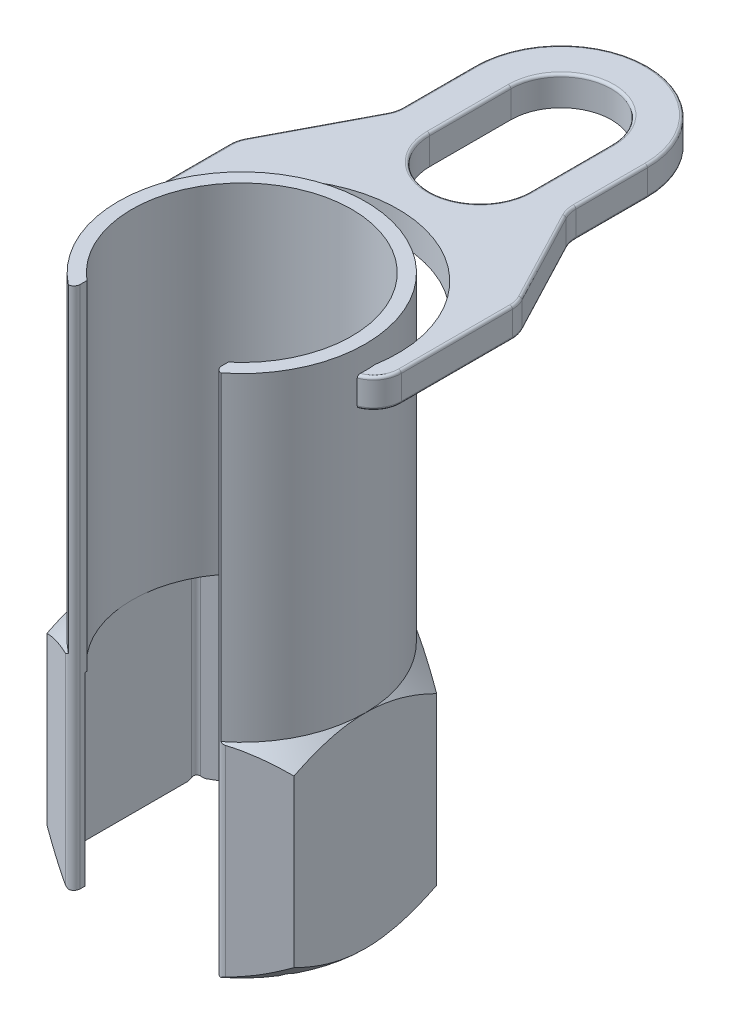
SolidWorks part; units mm, degrees
ref_plane "Front" through (0, 0, 0) normal (0, 0, 1) x (1, 0, 0)
ref_plane "Top" through (0, 0, 0) normal (0, 1, 0) x (1, 0, 0)
ref_plane "Right" through (0, 0, 0) normal (1, 0, 0) x (0, 0, -1)
sketch "Sketch1" plane through (0, 0, 0) normal (0, 1, 0) x (1, 0, 0)
  line L0 (-13.5, -16.0857) -> (-13.5, -19.4558)
  line L1 (0, 27.25) -> (-23.5992, 13.625)
  line L2 (0, 11.9615) -> (0, -7.933) construction
  line L3 (-23.5992, 13.625) -> (-23.5992, -13.625)
  line L4 (-23.5992, -13.625) -> (-13.5, -19.4558)
  line L5 (13.5, -19.4558) -> (23.5992, -13.625)
  line L6 (23.5992, -13.625) -> (23.5992, 13.625)
  line L7 (23.5992, 13.625) -> (0, 27.25)
  line L8 (13.5, -16.0857) -> (13.5, -19.4558)
  arc A0 (13.5, -19.3564) -> (-13.5, -19.3564) centre (0, 0) ccw construction
  arc A1 (13.5, -16.0857) -> (-13.5, -16.0857) centre (0, 0) ccw
  point P18 (-23.5992, -13.625)
  point P26 (23.5992, 13.625)
  dimension "D" = 54.5
  dimension "D2" = 42
  dimension "C" = 27
extrude "Extrude1" add sketch "Sketch1" along normal blind 39
sketch "Sketch3" plane through (0, 39, 0) normal (0, 1, 0) x (-1, 0, 0)
  line L0 (-23.5992, 13.625) -> (-23.5992, -13.625) construction
  line L2 (-13.5, 19.3563) -> (-13.5, 16.0857)
  line L3 (13.5, 19.3563) -> (13.5, 16.0857)
  arc A0 (-13.5, 16.0857) -> (13.5, 16.0857) centre (0, 0) ccw
  arc A1 (-13.5, 16.0857) -> (13.5, 16.0857) centre (0, 0) ccw construction
  arc A2 (-13.5, 19.3563) -> (13.5, 19.3563) centre (0, 0) ccw
  dimension "D1" = 0.0001
extrude "Extrude2" add sketch "Sketch3" along normal blind 61
sketch "Sketch8" plane through (0, 0, 0) normal (0, -1, 0) x (1, 0, 0)
  line L1 (23.5992, 13.625) -> (23.5992, -13.625) construction
  circle A0 centre (0, 0) radius 23.5992
extrude "Cut-Extrude4" cut sketch "Sketch8" against normal through all draft 45 flip side to cut
sketch "Sketch19" plane through (0, 39, 0) normal (0, 1, 0) x (-1, 0, 0)
  circle A1 centre (0, 0) radius 23.5991
  arc A2 (-13.5, 19.3563) -> (13.5, 19.3563) centre (0, 0) ccw construction
extrude "Cut-Extrude6" cut sketch "Sketch19" against normal through all draft 45 flip side to cut
sketch "Sketch26" plane through (0, 0, 0) normal (0, -1, 0) x (1, 0, 0)
  line L1 (-21, -12.1244) -> (0, -24.2487)
  line L2 (0, -24.2487) -> (21, -12.1244)
  line L3 (21, -12.1244) -> (21, 12.1244)
  line L4 (21, 12.1244) -> (0, 24.2487)
  line L5 (0, 24.2487) -> (-21, 12.1244)
  line L6 (-21, 12.1244) -> (-21, -12.1244)
  circle A0 centre (0, 0) radius 21 construction
  dimension "D1" = 42
extrude "Cut-Extrude9" cut sketch "Sketch26" against normal up to vertex (38.5 mm away)
fillet "Fillet1" radius 1.2 7 edges at (-21, 17.9993, -12.1244) (-21, 17.9993, 12.1244) (21, 17.9993, 12.1244) (21, 17.9993, -12.1244) (-13.5, 19.4999, 19.4558) (13.5, 19.5, 19.4558) (0, 17.9993, -24.2487)
sketch "Sketch4" [suppressed] plane through (0, 0, 0) normal (0, 1, 0) x (-1, 0, 0)
  line L0 (0, -11.2014) -> (0, 12.8888) construction
  line L1 (-10, -2.5) -> (10, -2.5)
  line L2 (-10, -2.5) -> (-10, 3.8)
  line L3 (-10, 3.8) -> (10, 3.8)
  line L4 (10, -2.5) -> (10, 3.8)
  line L5 (16.2585, 0) -> (-21.4153, 0) construction
  dimension "D1" = 42
  dimension "D2" = 8
  dimension "D3" = 6.7
sketch "Sketch12" [suppressed] plane through (0, 0, 0) normal (0, 1, 0) x (1, 0, 0)
  line L0 (-11, -4) -> (11, -4)
  line L1 (0, 0) -> (-11.4274, 0) construction
  line L2 (-11, 2.7) -> (11, 2.7)
  line L3 (-4.5, 14.3091) -> (4.5, 14.3091)
  line L4 (-7, 3.2909) -> (-7, -3.2909) construction
  line L5 (7, -3.2909) -> (7, 3.2909) construction
  arc A0 (-11, -4) -> (11, -4) centre (0, 0) ccw
  arc A1 (-6.3246, -3) -> (6.3246, -3) centre (0, 0) ccw construction
  arc A2 (-4.5, 14.3091) -> (-11, 2.7) centre (2.617, 2.7) ccw
  arc A3 (-4.5, 14.3091) -> (4.5, 14.3091) centre (0, 0) ccw construction
  arc A4 (4.5, 14.3091) -> (11, 2.7) centre (-2.617, 2.7) cw
ref_plane "Plane3" through (0, 90, 0) normal (0, 1, 0) x (-1, 0, 0)
sketch "Sketch16" plane through (0, 90, 0) normal (0, 1, 0) x (-1, 0, 0)
  line L5 (0, 0) -> (0, 54.2988) construction
  line L6 (-16.5, -61) -> (-16.5, -47.3067)
  line L10 (16.5, -47.3067) -> (16.5, -61)
  line L11 (26.3926, -27.1569) -> (17.1074, -44.8431)
  line L12 (-26.3926, -27.1569) -> (-17.1074, -44.8431)
  line L13 (-27, -3.4661) -> (-27, -24.6933)
  line L14 (27, -3.4661) -> (27, -24.6933)
  line L15 (38.3763, 1.5) -> (-38.1367, 1.5) construction
  arc A0 (-14.5633, 18.5695) -> (14.5633, 18.5695) centre (0, 0) ccw construction
  arc A1 (-23.5514, 1.5) -> (23.5514, 1.5) centre (0, 0) ccw
  arc A2 (27, -3.4661) -> (23.5514, 1.5) centre (21.7, -3.4661) ccw
  arc A3 (-27, -3.4661) -> (-23.5514, 1.5) centre (-21.7, -3.4661) cw
  arc A4 (-27, -24.6933) -> (-26.3926, -27.1569) centre (-21.7, -24.6933) ccw
  arc A5 (-17.1074, -44.8431) -> (-16.5, -47.3067) centre (-21.8, -47.3067) cw
  arc A7 (27, -24.6933) -> (26.3926, -27.1569) centre (21.7, -24.6933) cw
  arc A8 (17.1074, -44.8431) -> (16.5, -47.3067) centre (21.8, -47.3067) ccw
  arc A15 (16.5, -61) -> (-16.5, -61) centre (0, -61) cw
  point P18 (-27, -26)
  point P22 (-16.5, -46)
  point P25 (27, -26)
  point P30 (16.5, -46)
  dimension "D1" = 54
  dimension "D2" = 26
  dimension "D3" = 46
  dimension "D4" = 5.3
  dimension "D6" = 33
  dimension "D7" = 61
  dimension "D14" = 1.5
extrude "Extrude7" add sketch "Sketch16" along normal blind 5.6
sketch "Sketch25" plane through (0, 95.6, 0) normal (0, -1, 0) x (1, 0, 0)
  line L1 (-29.4486, 0) -> (37.9585, 0) construction
  line L3 (0, -57.3769) -> (0, 10.8445) construction
  line L4 (-9.6, -61) -> (-9.6, -45.5)
  line L5 (9.6, -61) -> (9.6, -45.5)
  arc A0 (-14.5633, 18.5695) -> (14.5633, 18.5695) centre (0, 0) ccw construction
  arc A2 (-16.5, -61) -> (16.5, -61) centre (0, -61) ccw construction
  arc A6 (23.5142, -2) -> (-23.5142, -2) centre (0, 0) cw
  arc A7 (23.5142, -2) -> (-23.5142, -2) centre (0, -6) cw
  arc A8 (9.6, -61) -> (-9.6, -61) centre (0, -61) cw
  arc A9 (9.6, -45.5) -> (-9.6, -45.5) centre (0, -45.5) ccw
  dimension "D1" = 32
  dimension "D2" = 19.2
  dimension "D3" = 2
  dimension "D4" = 6
extrude "Cut-Extrude8" cut sketch "Sketch25" along normal up to next
fillet "Fillet4" radius 0.5 30 edges at (9.6, 95.6, -53.25) (0, 95.6, -70.6) (-9.6, 95.6, -53.25) (26.0533, 95.6, -0.4431) (27, 95.6, -14.0797) (26.8459, 95.6, -25.962) (-26.0533, 95.6, -0.4431) (-27, 95.6, -14.0797) (-26.8459, 95.6, -25.962) (-21.75, 95.6, -36) (-16.6541, 95.6, -46.038) (-16.5, 95.6, -54.1533) (0, 95.6, -77.5) (16.5, 95.6, -54.1533) (16.6541, 95.6, -46.038) (26.0533, 90, -0.4431) (27, 90, -14.0797) (26.8459, 90, -25.962) (-26.0533, 90, -0.4431) (-27, 90, -14.0797) (-26.8459, 90, -25.962) (-21.75, 90, -36) (-16.6541, 90, -46.038) (-16.5, 90, -54.1533) (0, 90, -77.5) (16.5, 90, -54.1533) (16.6541, 90, -46.038) (0, 95.6, -35.9) (21.75, 95.6, -36) (21.75, 90, -36)
sketch "Sketch20" [suppressed] plane through (0, 0, 0) normal (0, 1, 0) x (1, 0, 0)
  line L0 (0, 0) -> (0, 12.8849) construction
  line L1 (-7.5, -9.3675) -> (-7.5, -14.4157)
  line L2 (7.5, -9.3675) -> (7.5, -14.4157)
  arc A0 (7.5, -14.4157) -> (-7.5, -14.4157) centre (0, 0) ccw
  arc A1 (7.5, -9.3675) -> (-7.5, -9.3675) centre (0, 0) ccw
  circle A2 centre (0, 0) radius 16.25 construction
  circle A3 centre (0, 0) radius 12 construction
  dimension "D1" = 54.5
  dimension "D2" = 42
  dimension "D3" = 27
extrude "Extrude3" [suppressed] add sketch "Sketch20" along normal blind 56
ref_plane "Plane7" [suppressed] through (0, 41.999, 0) normal (0, 1, 0) x (-1, 0, 0)
sketch "Sketch21" [suppressed] plane through (0, 41.999, 0) normal (0, 1, 0) x (-1, 0, 0)
  line L1 (2.5, 16.0565) -> (2.5, 19.8734)
  line L2 (7.5, 14.4157) -> (7.5, 9.3675) construction
  line L4 (7.5, 14.4157) -> (7.5, 18.5729)
  arc A1 (2.5, 16.0565) -> (7.5, 14.4157) centre (0, 0) ccw
  arc A2 (2.5, 19.8734) -> (7.5, 18.5729) centre (0, 0) ccw
  arc A3 (-7.5, 14.4157) -> (7.5, 14.4157) centre (0, 0) ccw construction
  dimension "D1" = 5.04
  dimension "D2" = 2.5
extrude "Extrude4" [suppressed] add sketch "Sketch21" against normal blind 16.5 separate body
ref_plane "Plane6" [suppressed] through (5.0421, 41.999, -19.385) normal (0.2517, 0, -0.9678) x (-0.9678, 0, -0.2517)
sketch "Sketch22" [suppressed] plane through (5.0421, 41.999, -19.385) normal (0.2517, 0, -0.9678) x (-0.9678, 0, -0.2517)
  line L0 (20.03, 0) -> (-20.03, 0) construction
  line L1 (0, 0) -> (0, 14.8678) construction
  line L2 (-3.2, -3.3) -> (3.2, -3.3)
  line L3 (-3.2, -3.3) -> (-3.2, -9.7)
  line L4 (-3.2, -9.7) -> (3.2, -9.7)
  line L5 (3.2, -3.3) -> (3.2, -9.7)
  line L7 (-18.9345, -6.5) -> (19.4735, -6.5) construction
  dimension "D1" = 9.2
  dimension "D2" = 8.25
  dimension "D3" = 9.2
extrude "Extrude5" [suppressed] add sketch "Sketch22" along normal blind 19 and the other way up to next
sketch "Sketch23" [suppressed] plane through (8.0628, 0, -30.9986) normal (0.2517, 0, -0.9678) x (-0.9678, 0, -0.2517)
  circle A0 centre (0, 35.499) radius 4.5255
extrude "Extrude6" [suppressed] add sketch "Sketch23" along normal blind 46 draft 2
dome "Dome1" [suppressed] faces to dome 1 distance 3 parameters "D1"=3
sketch "Sketch24" [suppressed] plane through (0, 0, 0) normal (0, -1, 0) x (1, 0, 0)
  line L2 (-12, 6.9282) -> (-12, -6.9282)
  line L3 (-12, -6.9282) -> (0, -13.8564)
  line L4 (0, -13.8564) -> (12, -6.9282)
  line L5 (12, -6.9282) -> (12, 6.9282)
  line L6 (12, 6.9282) -> (0, 13.8564)
  line L7 (0, 13.8564) -> (-12, 6.9282)
  circle A0 centre (0, 0) radius 12 construction
  dimension "D1" = 42
extrude "Cut-Extrude7" [suppressed] cut sketch "Sketch24" against normal through all
fillet "Fillet2" [suppressed] radius 0.5
fillet "Fillet3" [suppressed] radius 0.5
fillet "Fillet5" [suppressed] radius 1
